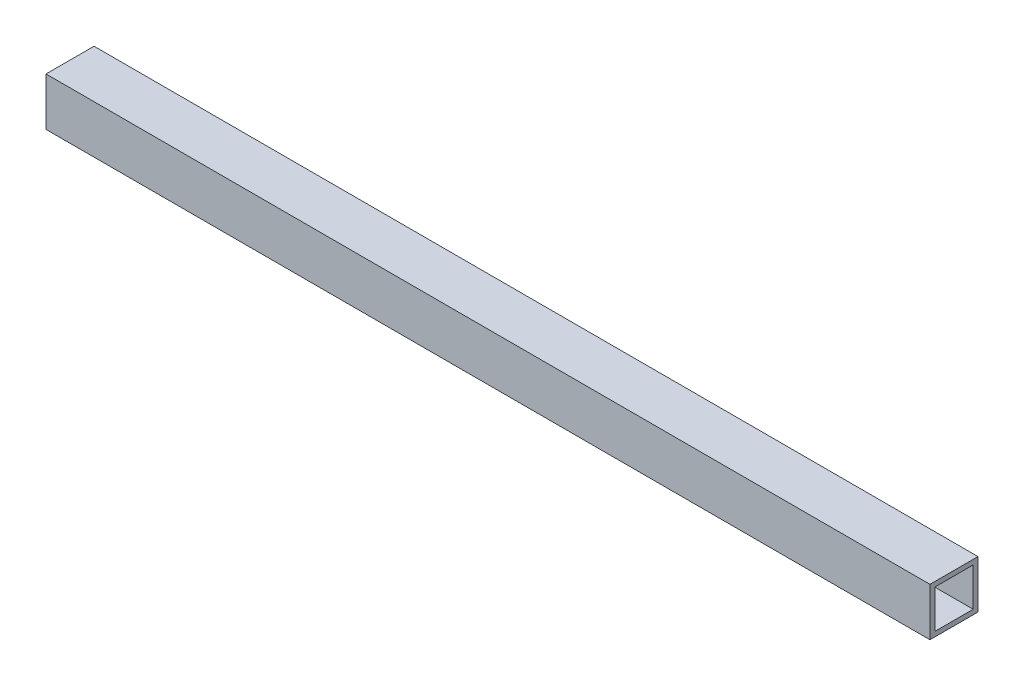
SolidWorks part; units mm, degrees
ref_plane "Front Plane" through (0, 0, 0) normal (0, 0, 1) x (1, 0, 0)
ref_plane "Top Plane" through (0, 0, 0) normal (0, 1, 0) x (1, 0, 0)
ref_plane "Right Plane" through (0, 0, 0) normal (1, 0, 0) x (0, 0, -1)
sketch "Sketch1" plane through (0, 0, 0) normal (1, 0, 0) x (0, 0, -1)
  line L1 (0, 0) -> (25.4, 0)
  line L2 (0, 0) -> (0, 25.4)
  line L3 (0, 25.4) -> (25.4, 25.4)
  line L4 (25.4, 0) -> (25.4, 25.4)
  dimension "D1" = 25.4
  dimension "D2" = 25.4
extrude "Extrude-Thin1" add sketch "Sketch1" along normal blind 584.2 thin
